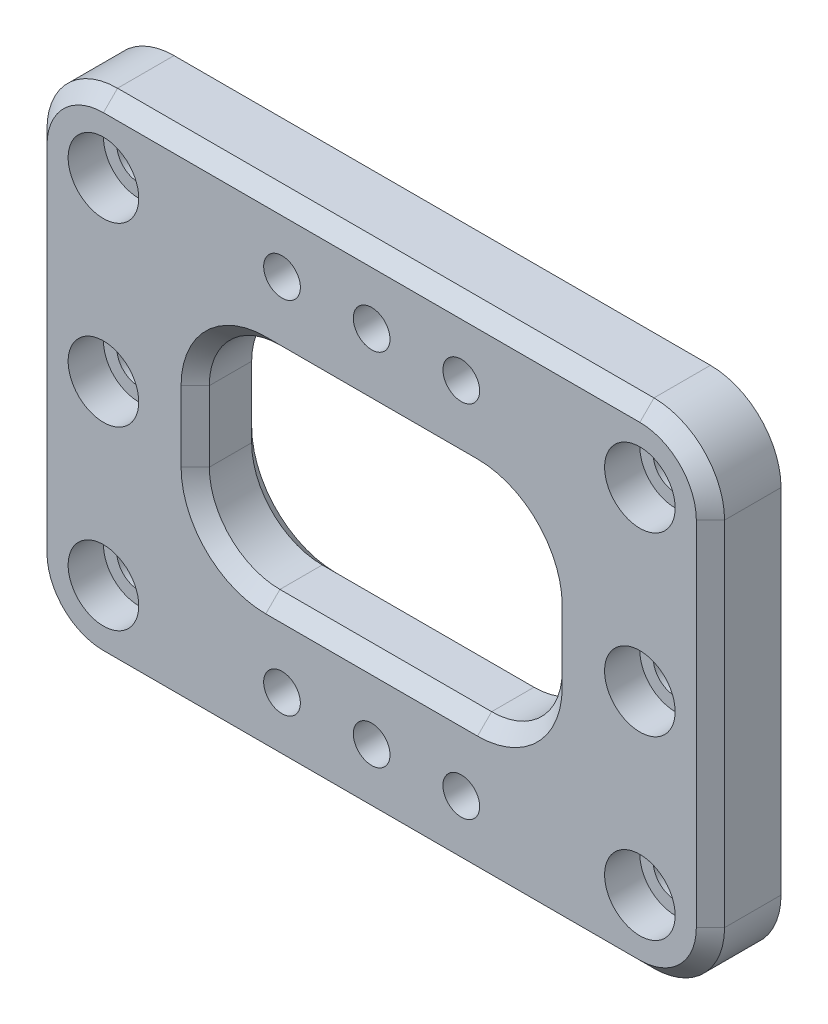
SolidWorks part; units mm, degrees
material "ABS"
ref_plane "前视基准面" through (0, 0, 0) normal (0, 0, 1) x (1, 0, 0)
ref_plane "上视基准面" through (0, 0, 0) normal (0, 1, 0) x (1, 0, 0)
ref_plane "右视基准面" through (0, 0, 0) normal (1, 0, 0) x (0, 0, -1)
sketch "草图1" plane through (0, 0, 0) normal (0, 0, 1) x (1, 0, 0)
  line L1 (-48, 35) -> (48, 35)
  line L2 (-48, 35) -> (-48, -35)
  line L3 (-48, -35) -> (48, -35)
  line L4 (48, 35) -> (48, -35)
  line L5 (-48, 35) -> (48, -35) construction
  line L6 (-48, -35) -> (48, 35) construction
  point P0 (0, 0)
extrude "凸台-拉伸1" add sketch "草图1" along normal blind 10
fillet "圆角1" radius 10 4 edges at (48, -35, 5) (-48, -35, 5) (48, 35, 5) (-48, 35, 5)
sketch "草图2" plane through (0, 0, 10) normal (0, 0, 1) x (1, 0, 0)
  line L0 (0, 35) -> (0, 25.5) construction
  line L1 (38, 35) -> (-38, 35) construction
  line L2 (0, 25.5) -> (-12.7, 25.5) construction
  line L3 (0, 25.5) -> (0, -25.5) construction
  line L4 (0, -25.5) -> (-12.7, -25.5) construction
  line L5 (0, -25.5) -> (12.7, -25.5) construction
  circle A0 centre (0, 25.5) radius 2.6
  circle A1 centre (-12.7, 25.5) radius 2.6
  circle A2 centre (12.7, 25.5) radius 2.6
  circle A3 centre (-12.7, -25.5) radius 2.6
  circle A4 centre (0, -25.5) radius 2.6
  circle A5 centre (12.7, -25.5) radius 2.6
  point P16 (0, 0)
  dimension "D1" = 12.7
  dimension "D2" = 0
extrude "切除-拉伸1" cut sketch "草图2" against normal blind 10
sketch "草图3" plane through (0, 0, 10) normal (0, 0, 1) x (1, 0, 0)
  line L0 (-48, 0) -> (-38, 0) construction
  line L1 (-48, 25) -> (-48, -25) construction
  line L2 (-38, 0) -> (-38, 25) construction
  line L3 (-38, 0) -> (-38, -25) construction
  line L4 (0, 0) -> (0, 10) construction
  circle A0 centre (-38, 25) radius 5
  circle A1 centre (-38, 0) radius 5
  circle A2 centre (-38, -25) radius 5
  circle A3 centre (38, -25) radius 5
  circle A4 centre (38, 0) radius 5
  circle A5 centre (38, 25) radius 5
extrude "切除-拉伸2" cut sketch "草图3" against normal blind 5
sketch "草图4" plane through (0, 0, 5) normal (0, 0, 1) x (1, 0, 0)
  circle A0 centre (-38, 25) radius 3.1
  circle A1 centre (-38, 0) radius 3.1
  circle A2 centre (-38, -25) radius 3.1
  circle A3 centre (38, 25) radius 3.1
  circle A4 centre (38, 0) radius 3.1
  circle A5 centre (38, -25) radius 3.1
extrude "切除-拉伸3" cut sketch "草图4" against normal blind 5
chamfer "倒角1" distance 1 angle 45 6 edges at (41.1, 25, 0) (41.1, 0, 0) (41.1, -25, 0) (-34.9, -25, 0) (-34.9, 0, 0) (-34.9, 25, 0)
chamfer "倒角2" distance 2 angle 45 8 edges at (48, 0, 10) (45.0711, 32.0711, 10) (45.0711, -32.0711, 10) (0, 35, 10) (0, -35, 10) (-45.0711, 32.0711, 10) (-45.0711, -32.0711, 10) (-48, 0, 10)
sketch "草图5" plane through (0, 0, 10) normal (0, 0, 1) x (1, 0, 0)
  line L1 (-25, -15) -> (25, -15)
  line L2 (-25, -15) -> (-25, 15)
  line L3 (-25, 15) -> (25, 15)
  line L4 (25, -15) -> (25, 15)
  line L5 (-25, -15) -> (25, 15) construction
  line L6 (-25, 15) -> (25, -15) construction
  point P0 (0, 0)
extrude "切除-拉伸4" cut sketch "草图5" against normal blind 10
fillet "圆角2" radius 10 4 edges at (25, -15, 5) (25, 15, 5) (-25, -15, 5) (-25, 15, 5)
chamfer "倒角3" distance 2 angle 45 16 edges at (22.0711, -12.0711, 0) (22.0711, 12.0711, 0) (0, -15, 0) (0, 15, 0) (-22.0711, -12.0711, 0) (-22.0711, 12.0711, 0) (22.0711, -12.0711, 10) (0, -15, 10) (22.0711, 12.0711, 10) (-22.0711, -12.0711, 10) (0, 15, 10) (-22.0711, 12.0711, 10) (25, 0, 0) (-25, 0, 0) (25, 0, 10) (-25, 0, 10)
